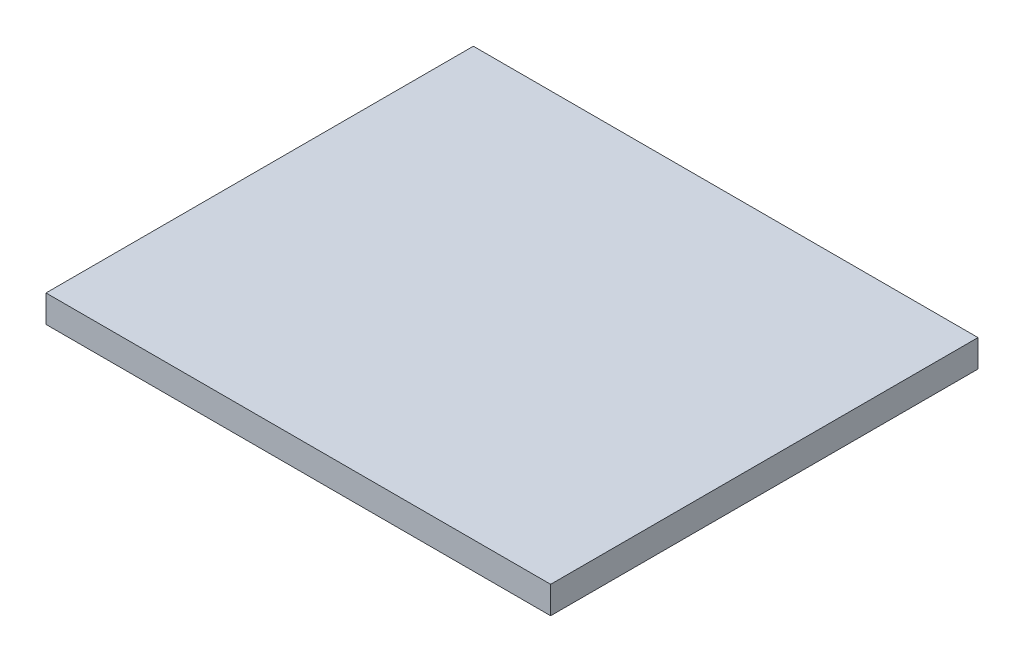
SolidWorks part; units mm, degrees
material "Acrylic (Medium-high impact)"
ref_plane "Front Plane" through (0, 0, 0) normal (0, 0, 1) x (1, 0, 0)
ref_plane "Top Plane" through (0, 0, 0) normal (0, 1, 0) x (1, 0, 0)
ref_plane "Right Plane" through (0, 0, 0) normal (1, 0, 0) x (0, 0, -1)
sketch "Sketch1" plane through (0, 0, 0) normal (0, 1, 0) x (1, 0, 0)
  line L1 (0, 0) -> (111, 0)
  line L2 (0, 0) -> (0, 94)
  line L3 (0, 94) -> (111, 94)
  line L4 (111, 0) -> (111, 94)
  dimension "D1" = 94
  dimension "D2" = 111
extrude "Boss-Extrude1" add sketch "Sketch1" along normal blind 6
